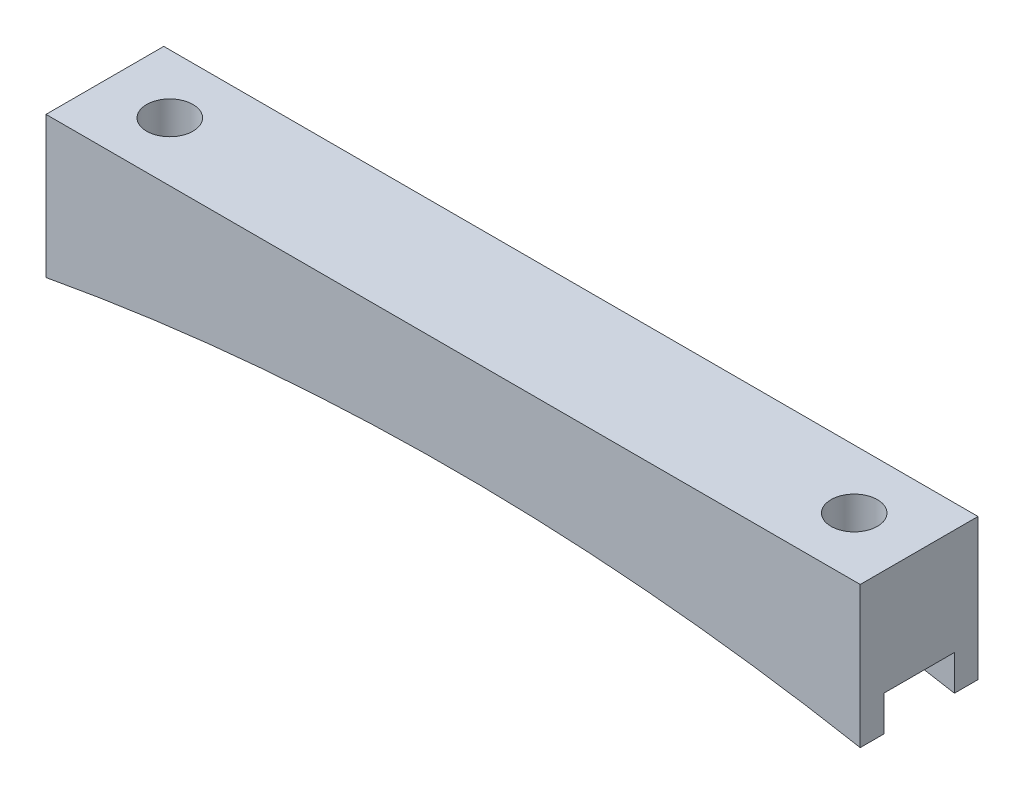
SolidWorks part; units mm, degrees
ref_plane "Front Plane" through (0, 0, 0) normal (0, 0, 1) x (1, 0, 0)
ref_plane "Top Plane" through (0, 0, 0) normal (0, 1, 0) x (1, 0, 0)
ref_plane "Right Plane" through (0, 0, 0) normal (1, 0, 0) x (0, 0, -1)
sketch "Sketch1" plane through (0, 0, 0) normal (0, 0, 1) x (1, 0, 0)
  line L0 (-43.905, 0) -> (43.905, 0)
  line L1 (-36.905, -2.54) -> (36.905, -2.54) construction
  line L2 (0, 0) -> (0, -4.6068) construction
  line L3 (43.905, 0) -> (43.905, -15.24)
  line L4 (-43.905, 0) -> (-43.905, -15.24)
  arc A0 (-43.905, -15.24) -> (43.905, -15.24) centre (0, -252.5121) cw
  point P4 (0, 0)
  point P9 (0, -2.54)
  dimension "D4" = 241.3
  dimension "D1" = 73.81
  dimension "D2" = 2.54
  dimension "D3" = 7
  dimension "D5" = 15.24
extrude "Boss-Extrude1" add sketch "Sketch1" along normal blind 12.7
sketch "Sketch2" plane through (0, 0, 0) normal (0, 1, 0) x (1, 0, 0)
  line L1 (-36.905, 0) -> (-36.905, -12.7) construction
  line L2 (-43.905, 0) -> (43.905, 0) construction
  line L3 (43.905, -12.7) -> (-43.905, -12.7) construction
  line L4 (36.905, 0) -> (36.905, -12.7) construction
  circle A0 centre (-36.905, -6.35) radius 2.5
  circle A1 centre (36.905, -6.35) radius 2.5
  circle A2 centre (-36.905, -6.35) radius 3 construction
  point P7 (-36.905, -6.35)
  dimension "D1" = 5
  dimension "D2" = 6
extrude "Cut-Extrude1" cut sketch "Sketch2" against normal through all
sketch "Sketch3" plane through (43.905, 0, 0) normal (1, 0, 0) x (0, 0, -1)
  line L0 (-12.7, -15.24) -> (0, -15.24) construction
  line L1 (-10.16, -15.24) -> (-2.54, -15.24)
  line L2 (-10.16, -15.24) -> (-10.16, -11.43)
  line L3 (-10.16, -11.43) -> (-2.54, -11.43)
  line L4 (-2.54, -15.24) -> (-2.54, -11.43)
  line L5 (-12.7, -15.24) -> (-12.7, 0) construction
  line L6 (0, -15.24) -> (0, 0) construction
  dimension "D1" = 2.54
  dimension "D2" = 2.54
  dimension "D3" = 3.81
extrude "Cut-Extrude2" cut sketch "Sketch3" against normal through all
